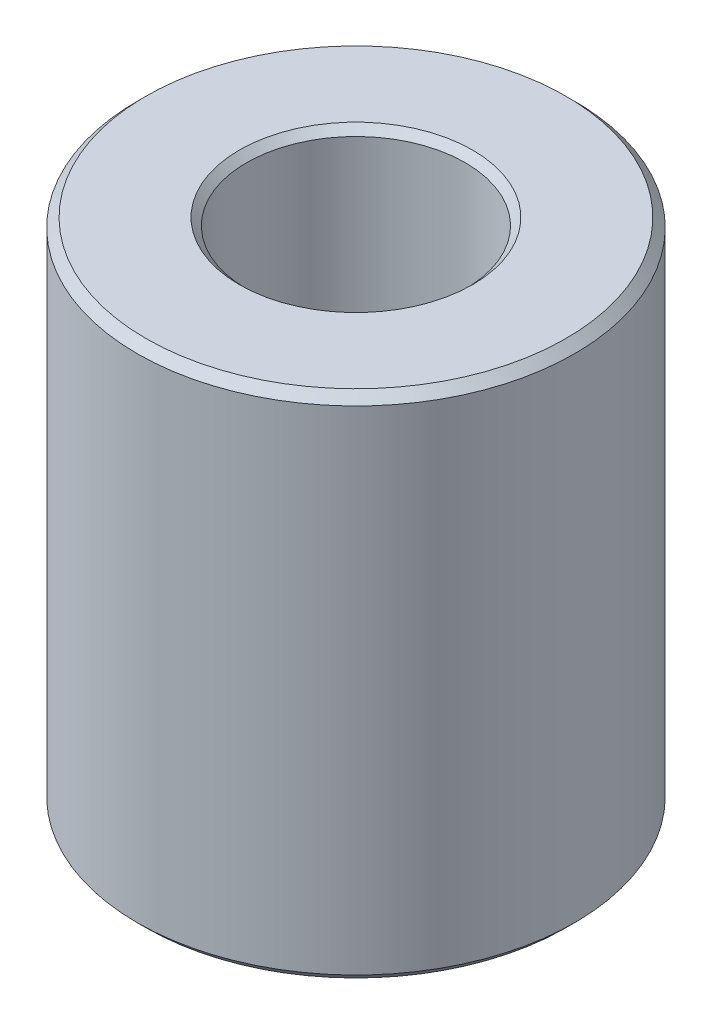
SolidWorks part; units mm, degrees
material "Brass"
ref_plane "Front" through (0, 0, 0) normal (0, 0, 1) x (1, 0, 0)
ref_plane "Top" through (0, 0, 0) normal (0, 1, 0) x (1, 0, 0)
ref_plane "Right" through (0, 0, 0) normal (1, 0, 0) x (0, 0, -1)
sketch "Sketch1" plane through (0, 0, 0) normal (0, 1, 0) x (1, 0, 0)
  circle A0 centre (0, 0) radius 19.05
  dimension "D1" = 38.1
extrude "Extrude1" add sketch "Sketch1" along normal blind 44.45
hole_wizard "3/8 (0.375) Diameter Hole1" positions "Sketch3" profile "Sketch2" hole size "3/8" standard "Ansi Inch" end condition through all
sketch "Sketch3" plane through (0, 44.45, 0) normal (0, 1, 0) x (-1, 0, 0)
  point P0 (0, 0)
sketch "Sketch2" plane through (0, 44.45, 0) normal (1, 0, 0) x (0, 0, 1)
  line L0 (0, 0) -> (0, 44.45)
  line L1 (0, 44.45) -> (5.4102, 44.45)
  line L2 (4.7752, 43.815) -> (4.7752, 0)
  line L5 (4.7752, 0) -> (0, 0)
  line L7 (5.4102, 44.45) -> (4.7752, 43.815)
  line L8 (-5.4102, 44.45) -> (-4.7752, 43.815) construction
  line L11 (0, -6.35) -> (0, 107.95) construction
  dimension "Thru Hole Dia." = 9.5504
  dimension "Thru Hole Depth" = 44.45
  dimension "Far C'Sink Dia." = 10.8204
  dimension "Far C'Sink Angle" = 90
chamfer "Chamfer1" distance 0.762 angle 45 2 edges at (0, 0, 19.05) (0, 44.45, 19.05)
hole_wizard "3/4 (0.75) Diameter Hole1" positions "Sketch5" profile "Sketch4" hole size "3/4" standard "Ansi Inch"
sketch "Sketch5" plane through (0, 44.45, 0) normal (0, 1, 0) x (-1, 0, 0)
  point P0 (0, 0)
sketch "Sketch4" plane through (0, 44.45, 0) normal (1, 0, 0) x (0, 0, 1)
  line L0 (0, 0) -> (0, 36.068)
  line L1 (0, 36.068) -> (9.525, 36.068)
  line L2 (9.525, 36.068) -> (9.525, 0.635)
  line L3 (9.525, 0.635) -> (10.16, 0)
  line L5 (10.16, 0) -> (0, 0)
  line L6 (-9.525, 0.635) -> (-10.16, 0) construction
  line L10 (0, 36.068) -> (-9.525, 36.068) construction
  line L11 (0, -6.35) -> (0, 107.95) construction
  dimension "Hole Dia." = 19.05
  dimension "Hole Depth" = 36.068
  dimension "Near C'Sink Dia." = 20.32
  dimension "Near C'Sink Angle" = 90
  dimension "Drill Angle" = 180
chamfer "Chamfer2" distance 0.254 angle 45 1 edges at (0, 8.382, 9.525)
